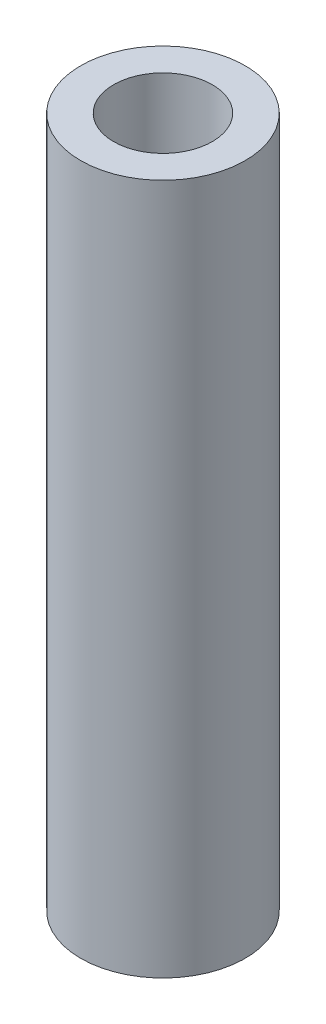
SolidWorks part; units mm, degrees
ref_plane "Front Plane" through (0, 0, 0) normal (0, 0, 1) x (1, 0, 0)
ref_plane "Top Plane" through (0, 0, 0) normal (0, 1, 0) x (1, 0, 0)
ref_plane "Right Plane" through (0, 0, 0) normal (1, 0, 0) x (0, 0, -1)
sketch "Sketch1" plane through (0, 0, 0) normal (0, 1, 0) x (1, 0, 0)
  circle A0 centre (0, 0) radius 9.525
  circle A1 centre (0, 0) radius 15.875
  dimension "D1" = 31.75
  dimension "D2" = 19.05
extrude "Boss-Extrude1" add sketch "Sketch1" along normal blind 133.35
